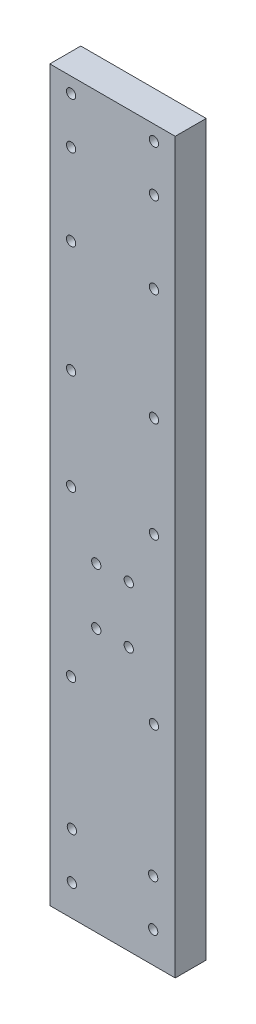
SolidWorks part; units mm, degrees
ref_plane "Front Plane" through (0, 0, 0) normal (0, 0, 1) x (1, 0, 0)
ref_plane "Top Plane" through (0, 0, 0) normal (0, 1, 0) x (1, 0, 0)
ref_plane "Right Plane" through (0, 0, 0) normal (1, 0, 0) x (0, 0, -1)
sketch "Sketch3" plane through (0, 0, 0) normal (0, 0, 1) x (1, 0, 0)
  line L0 (0, 94.0064) -> (0, -0.1536)
  line L1 (16.2, 94.0064) -> (16.2, -0.1536)
  line L2 (0, -0.1536) -> (16.2, -0.1536)
  line L4 (0, 94.0064) -> (16.2, 94.0064)
  line L5 (0, 12.3464) -> (16.2, 12.3464) construction
  line L6 (0, 58.6064) -> (16.2, 58.6064) construction
  line L26 (0, 50.6064) -> (16.2, 50.6064) construction
  line L27 (0, 24.3464) -> (16.2, 24.3464) construction
  line L30 (0, 78.0614) -> (16.2, 78.0614) construction
  line L32 (0, 84.0614) -> (16.2, 84.0614) construction
  circle A0 centre (6, 33.8464) radius 0.6
  circle A1 centre (10.2, 33.8464) radius 0.6
  circle A2 centre (2.75, 86.0614) radius 0.6
  circle A3 centre (10.2, 41.1664) radius 0.6
  circle A4 centre (13.45, 48.1064) radius 0.6
  circle A5 centre (2.75, 92.0614) radius 0.6
  circle A6 centre (13.45, 86.0614) radius 0.6
  circle A7 centre (2.75, 61.1064) radius 0.6
  circle A16 centre (2.85, 9.8464) radius 0.6
  circle A17 centre (13.35, 9.8464) radius 0.6
  circle A18 centre (13.35, 3.8464) radius 0.6
  circle A19 centre (2.85, 3.8464) radius 0.6
  circle A20 centre (13.45, 61.1064) radius 0.6
  circle A21 centre (2.75, 75.5614) radius 0.6
  circle A22 centre (13.45, 26.8464) radius 0.6
  circle A23 centre (13.45, 75.5614) radius 0.6
  circle A24 centre (13.45, 92.0614) radius 0.6
  circle A25 centre (2.75, 26.8464) radius 0.6
  circle A26 centre (6, 41.1064) radius 0.6
  circle A27 centre (2.75, 48.1064) radius 0.6
  dimension "D1" = 2.5
  dimension "D2" = 9.5
  dimension "D32" = 6
  dimension "D33" = 6
  dimension "D45" = 1.2
  dimension "D3" = 2.5
  dimension "D4" = 9.5
  dimension "D5" = 6
  dimension "D6" = 2.75
  dimension "D7" = 2.75
  dimension "D8" = 6
  dimension "D9" = 2.5
  dimension "D10" = 2.5
  dimension "D11" = 9.5
  dimension "D12" = 9.44
  dimension "D13" = 2.75
  dimension "D14" = 6
  dimension "D15" = 2.75
  dimension "D16" = 6
  dimension "D17" = 12
  dimension "D18" = 2.5
  dimension "D19" = 4
  dimension "D20" = 6
  dimension "D21" = 6
  dimension "D22" = 4
  dimension "D23" = 2.85
  dimension "D24" = 2.85
  dimension "D25" = 26.26
  dimension "D26" = 16.2
  dimension "D27" = 8
  dimension "D28" = 2.5
  dimension "D29" = 2.5
  dimension "D30" = 2.75
  dimension "D31" = 2.75
  dimension "D34" = 2.5
  dimension "D35" = 2.5
  dimension "D36" = 2.75
  dimension "D37" = 2.75
  dimension "D38" = 19.455
  dimension "D39" = 6
  dimension "D40" = 2
  dimension "D41" = 2
  dimension "D42" = 2.75
  dimension "D43" = 2.75
  dimension "D44" = 2.5
  dimension "D46" = 2.75
  dimension "D47" = 2.75
  dimension "D48" = 9.945
extrude "Boss-Extrude3" add sketch "Sketch3" along normal blind 4
equation "\"D25@Sketch3\"= \"HL@parametersSketch@prostheticParameters.SLDPRT\" * 0.196 - 4 - 6'Index PIP length"
equation "\"D26@Sketch3\"= \"fingerWidth@parametersSketch@prostheticParameters.SLDPRT\"'Index Width"
equation "\"D38@Sketch3\"= \"HL@parametersSketch@prostheticParameters.SLDPRT\" * 0.143 - 3 - 4 'Index MIP Length"
equation "\"D48@Sketch3\"= \"HL@parametersSketch@prostheticParameters.SLDPRT\" * 0.097 - 3 - 5'Index DIP Length - Gap Fingertip"
equation "\"D45@Sketch3\"= 1 + \"tol1@parametersSketch@prostheticParameters.SLDPRT\""
